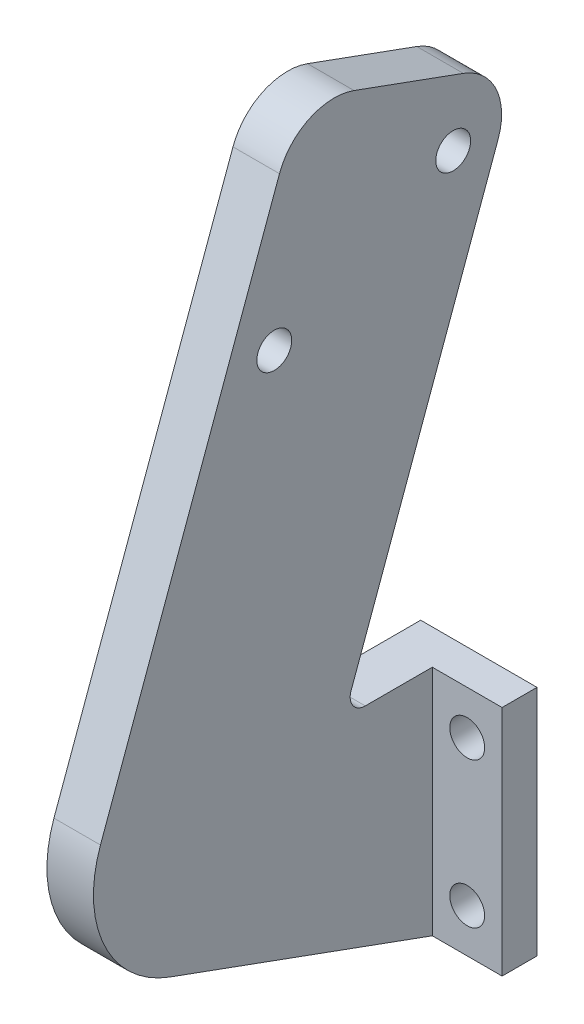
SolidWorks part; units mm, degrees
material "6061-T6 (SS)"
ref_plane "前视基准面" through (0, 0, 0) normal (0, 0, 1) x (1, 0, 0)
ref_plane "上视基准面" through (0, 0, 0) normal (0, 1, 0) x (1, 0, 0)
ref_plane "右视基准面" through (0, 0, 0) normal (1, 0, 0) x (0, 0, -1)
sketch "草图1" plane through (0, 0, 0) normal (0, 0, 1) x (1, 0, 0)
  line L1 (0, 0) -> (17, 0)
  line L2 (0, 0) -> (0, 20)
  line L3 (0, 20) -> (17, 20)
  line L4 (17, 0) -> (17, 20)
  circle A0 centre (3, 16.25) radius 1.5
  circle A1 centre (14, 16.25) radius 1.5
  circle A2 centre (14, 3.75) radius 1.5
  circle A3 centre (3, 3.75) radius 1.5
  dimension "D3" = 3
  dimension "D4" = 3.75
  dimension "D5" = 3
  dimension "D1" = 17
  dimension "D2" = 20
  dimension "D6" = 2
  dimension "D7" = 2
extrude "凸台-拉伸1" add sketch "草图1" along normal blind 3
ref_plane "基准面4" through (6, 0, 0) normal (-1, 0, 0) x (0, 0, 1)
sketch "草图3" plane through (6, 0, 0) normal (-1, 0, 0) x (0, 0, 1)
  line L0 (3, 20) -> (10.6191, 20)
  line L2 (14.4283, 68.0102) -> (34.9495, 11.6287)
  line L3 (34.9495, 11.6287) -> (3, 0)
  line L5 (3, 0) -> (0, 0) construction
  line L6 (3, 20) -> (3, 0) construction
  line L7 (3, 20) -> (3, 0)
  line L8 (10.6191, 20) -> (-4.3655, 61.1698)
  line L9 (-4.3655, 61.1698) -> (14.4283, 68.0102)
  dimension "D1" = 20
  dimension "D2" = 60
  dimension "D3" = 34
  dimension "D5" = 20
extrude "凸台-拉伸2" add sketch "草图3" against normal blind 5
sketch "草图4" plane through (11, 0, 0) normal (1, 0, 0) x (0, 0, -1)
  line L0 (-16.5865, 50.3855) -> (-5.3102, 46.2812) construction
  line L1 (-34.9495, 11.6287) -> (-14.4283, 68.0102) construction
  line L2 (-5.3102, 46.2812) -> (-1.206, 57.5575) construction
  line L3 (-14.4283, 68.0102) -> (4.3655, 61.1698) construction
  line L4 (4.3655, 61.1698) -> (-10.6191, 20) construction
  circle A0 centre (-16.5865, 50.3855) radius 1.5
  circle A1 centre (-1.206, 57.5575) radius 1.5
  dimension "D1" = 5.3
  dimension "D2" = 3
  dimension "D3" = 4
  dimension "D4" = 3
  dimension "D5" = 12
  dimension "D6" = 16
extrude "切除-拉伸1" cut sketch "草图4" against normal blind 5
fillet "圆角2" radius 5 2 edges at (8.5, 68.0102, 14.4283) (8.5, 61.1698, -4.3655)
fillet "圆角3" radius 1.3 1 edges at (8.5, 20, 10.6191)
fillet "圆角4" radius 10 1 edges at (8.5, 11.6287, 34.9495)
sketch "草图5" plane through (0, 0, 3) normal (0, 0, 1) x (1, 0, 0)
  line L1 (0, 20) -> (6, 20)
  line L2 (0, 20) -> (0, 0)
  line L3 (0, 0) -> (6, 0)
  line L4 (6, 20) -> (6, 0)
extrude "切除-拉伸2" cut sketch "草图5" against normal blind 10
sketch "草图6" plane through (6, 0, 0) normal (-1, 0, 0) x (0, 0, 1)
  line L7 (3, 0) -> (25.5526, 8.2085)
  line L8 (31.5293, 21.0256) -> (16.1384, 63.3118)
  line L9 (9.7299, 66.3001) -> (0.333, 62.8799)
  line L10 (-2.6554, 56.4714) -> (9.9841, 21.7446)
  line L11 (8.7625, 20) -> (0, 20)
  line L12 (0, 20) -> (0, 0)
  line L13 (0, 0) -> (3, 0)
  line L14 (3, 0) -> (25.5526, 8.2085)
  line L15 (31.5293, 21.0256) -> (16.1384, 63.3118)
  line L16 (9.7299, 66.3001) -> (0.333, 62.8799)
  line L17 (-2.6554, 56.4714) -> (9.9841, 21.7446)
  line L18 (8.7625, 20) -> (0, 20)
  line L19 (0, 20) -> (0, 0)
  line L20 (0, 0) -> (3, 0)
  circle A0 centre (16.5865, 50.3855) radius 1.5 construction
  circle A1 centre (1.206, 57.5575) radius 1.5 construction
  circle A2 centre (16.5865, 50.3855) radius 1.5
  circle A3 centre (1.206, 57.5575) radius 1.5
  arc A4 (25.5526, 8.2085) -> (31.5293, 21.0256) centre (22.1324, 17.6054) ccw
  arc A5 (16.1384, 63.3118) -> (9.7299, 66.3001) centre (11.44, 61.6017) ccw
  arc A6 (0.333, 62.8799) -> (-2.6554, 56.4714) centre (2.0431, 58.1815) ccw
  arc A7 (8.7625, 20) -> (9.9841, 21.7446) centre (8.7625, 21.3) ccw
  arc A8 (25.5526, 8.2085) -> (31.5293, 21.0256) centre (22.1324, 17.6054) ccw
  arc A9 (16.1384, 63.3118) -> (9.7299, 66.3001) centre (11.44, 61.6017) ccw
  arc A10 (0.333, 62.8799) -> (-2.6554, 56.4714) centre (2.0431, 58.1815) ccw
  arc A11 (8.7625, 20) -> (9.9841, 21.7446) centre (8.7625, 21.3) ccw
  dimension "D1" = 0
extrude "切除-拉伸3" cut sketch "草图6" against normal blind 1
